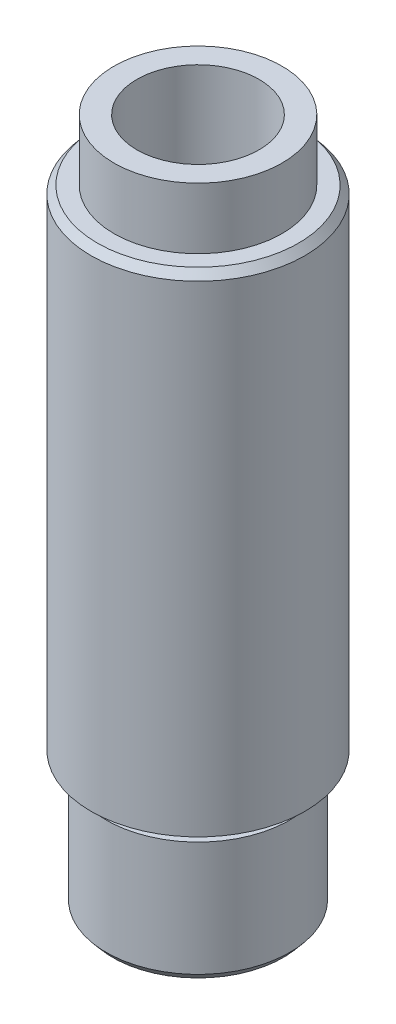
SolidWorks part; units mm, degrees
ref_plane "Alzado" through (0, 0, 0) normal (0, 0, 1) x (1, 0, 0)
ref_plane "Planta" through (0, 0, 0) normal (0, 1, 0) x (1, 0, 0)
ref_plane "Vista lateral" through (0, 0, 0) normal (1, 0, 0) x (0, 0, -1)
sketch "Croquis1" plane through (0, 0, 0) normal (0, 1, 0) x (1, 0, 0)
  circle A0 centre (0, 0) radius 7
  circle A1 centre (0, 0) radius 4
extrude "Saliente-Extruir1" add sketch "Croquis1" along normal blind 32
ref_plane "Plano1" through (0, 3, 0) normal (0, 1, 0) x (1, 0, 0)
sketch "Croquis2" plane through (0, 3, 0) normal (0, 1, 0) x (1, 0, 0)
  circle A0 centre (0, 0) radius 4 construction
  circle A1 centre (0, 0) radius 4
extrude "Saliente-Extruir2" add sketch "Croquis2" against normal blind 3
sketch "Croquis3" plane through (0, 0, 0) normal (0, -1, 0) x (-1, 0, 0)
  circle A0 centre (0, 0) radius 5.5
extrude "Saliente-Extruir3" add sketch "Croquis3" along normal blind 1
sketch "Croquis4" plane through (0, -1, 0) normal (0, -1, 0) x (1, 0, 0)
  circle A0 centre (0, 0) radius 6
extrude "Saliente-Extruir4" add sketch "Croquis4" along normal blind 8
sketch "Croquis5" plane through (0, -9, 0) normal (0, -1, 0) x (1, 0, 0)
  circle A0 centre (0, 0) radius 2
extrude "Cortar-Extruir1" cut sketch "Croquis5" against normal blind 34
chamfer "Chaflán1" distance 3 angle 35 1 edges at (0, -9, -2)
chamfer "Chaflán2" distance 0.5 angle 40 1 edges at (0, -9, -6)
chamfer "Chaflán3" distance 0.5 angle 40 1 edges at (0, 32, 7)
sketch "Croquis6" plane through (0, 32, 0) normal (0, 1, 0) x (1, 0, 0)
  circle A0 centre (0, 0) radius 5.5
  circle A1 centre (0, 0) radius 4 construction
  circle A2 centre (0, 0) radius 4
extrude "Saliente-Extruir5" add sketch "Croquis6" along normal blind 4
